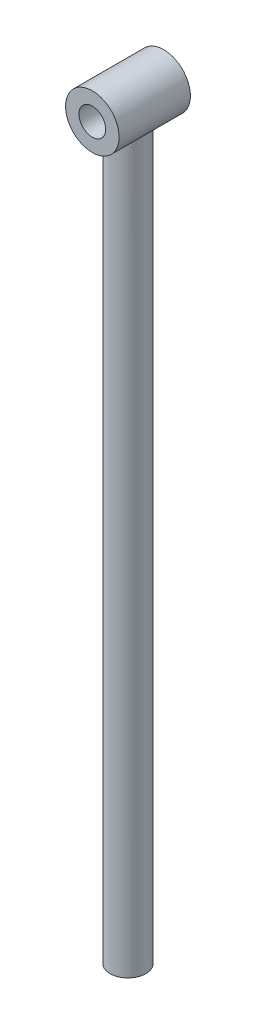
SolidWorks part; units mm, degrees
ref_plane "Front Plane" through (0, 0, 0) normal (0, 0, 1) x (1, 0, 0)
ref_plane "Top Plane" through (0, 0, 0) normal (0, 1, 0) x (1, 0, 0)
ref_plane "Right Plane" through (0, 0, 0) normal (1, 0, 0) x (0, 0, -1)
sketch "Sketch1" plane through (0, 0, 0) normal (0, 1, 0) x (1, 0, 0)
  circle A0 centre (0, 0) radius 20
  dimension "D1" = 40
extrude "Boss-Extrude1" add sketch "Sketch1" along normal mid plane 815
sketch "Sketch4" plane through (0, 0, 0) normal (0, 0, 1) x (1, 0, 0)
  circle A0 centre (0, 429.8607) radius 30
  circle A1 centre (0, 429.8607) radius 15
  point P3 (0, 0)
  dimension "D2" = 60
  dimension "D3" = 30
extrude "Boss-Extrude3" add sketch "Sketch4" along normal mid plane 80
